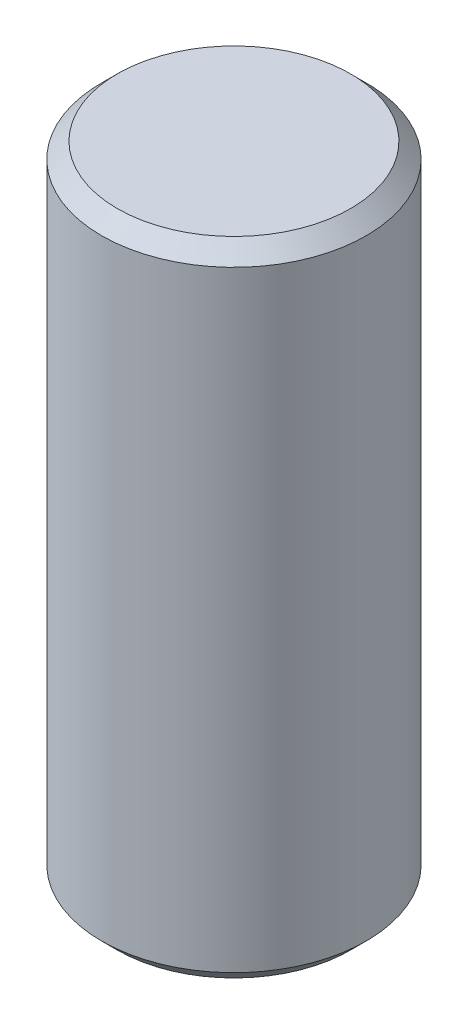
SolidWorks part; units mm, degrees
ref_plane "Front Plane" through (0, 0, 0) normal (0, 0, 1) x (1, 0, 0)
ref_plane "Top Plane" through (0, 0, 0) normal (0, 1, 0) x (1, 0, 0)
ref_plane "Right Plane" through (0, 0, 0) normal (1, 0, 0) x (0, 0, -1)
sketch "Sketch1" plane through (0, 0, 0) normal (0, 1, 0) x (1, 0, 0)
  circle A0 centre (0, 0) radius 429.26
  dimension "D1" = 858.52
extrude "Boss-Extrude1" add sketch "Sketch1" along normal blind 2082.8
chamfer "Chamfer2" distance 50.8 angle 45 2 edges at (0, 0, 429.26) (0, 2082.8, 429.26)
